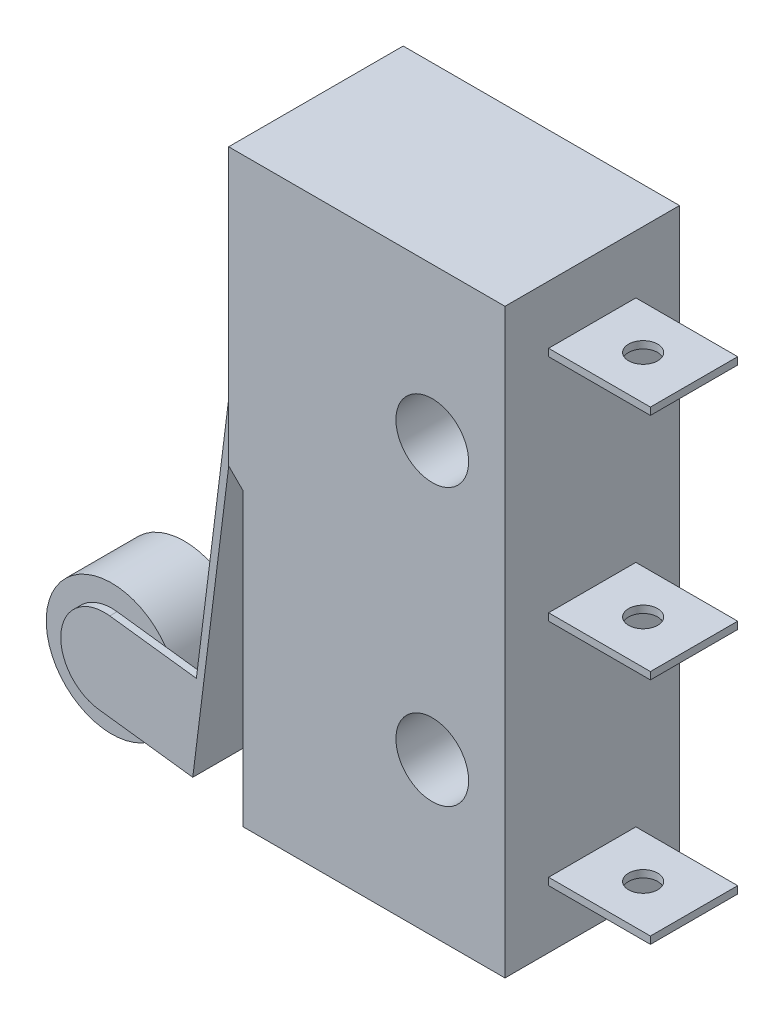
SolidWorks part; units mm, degrees
ref_plane "Front" through (0, 0, 0) normal (0, 0, 1) x (1, 0, 0)
ref_plane "Top" through (0, 0, 0) normal (0, 1, 0) x (1, 0, 0)
ref_plane "Right" through (0, 0, 0) normal (1, 0, 0) x (0, 0, -1)
sketch "Эскиз1" plane through (0, 0, 0) normal (0, 0, 1) x (1, 0, 0)
  line L0 (0, 0) -> (0, 10)
  line L1 (0, 0) -> (9, 0)
  line L2 (0, 20) -> (9, 20)
  line L3 (9, 0) -> (9, 20)
  line L4 (9, 10) -> (0, 10) construction
  line L5 (0, 10) -> (-0.5, 10.5)
  line L6 (-0.5, 10.5) -> (-0.5, 20)
  line L7 (0, 20) -> (-0.5, 20)
  circle A0 centre (6.5, 5.25) radius 1.25
  circle A1 centre (6.5, 14.75) radius 1.25
  dimension "D3" = 2.5
  dimension "D4" = 5.25
  dimension "D5" = 2.5
  dimension "D1" = 20
  dimension "D2" = 9
  dimension "D6" = 0.5
  dimension "D7" = 0.5
  dimension "D8" = 10
extrude "Бобышка-Вытянуть1" add sketch "Эскиз1" along normal blind 6
sketch "Эскиз2" plane through (-0.5, 0, 0) normal (-1, 0, 0) x (0, 0, 1)
  line L0 (3, 20) -> (3, 10.5) construction
  line L1 (6, 20) -> (0, 20) construction
  line L2 (6, 10.5) -> (0, 10.5) construction
ref_plane "Плоскость1" through (0, 0, 3) normal (0, 0, -1) x (0, -1, 0)
sketch "Эскиз3" plane through (0, 0, 3) normal (0, 0, -1) x (0, -1, 0)
  line L0 (-17, 0.5) -> (-17, 1.0293)
  line L1 (-20, 0.5) -> (-10.5, 0.5) construction
  line L2 (-13, 0.5) -> (-13, 1.75) construction
  line L3 (-16.781, 1.2774) -> (-13, 1.75)
  line L4 (-13, 1.75) -> (0.861, 3.4826)
  line L5 (0.861, 3.4826) -> (0.892, 3.2346)
  line L6 (0.892, 3.2346) -> (-16.531, 1.0567)
  line L7 (-16.75, 0.5) -> (-16.75, 0.8086)
  line L8 (-17, 0.5) -> (-16.75, 0.5)
  arc A0 (-16.781, 1.2774) -> (-17, 1.0293) centre (-16.75, 1.0293) ccw
  arc A1 (-16.531, 1.0567) -> (-16.75, 0.8086) centre (-16.5, 0.8086) ccw
  point P13 (-17, 1.25)
  dimension "D8" = 0.25
  dimension "D1" = 3
  dimension "D2" = 0.75
  dimension "D3" = 7
  dimension "D4" = 1.25
  dimension "D5" = 18
  dimension "D6" = 0.25
  dimension "D7" = 0.25
extrude "Бобышка-Вытянуть2" add sketch "Эскиз3" along normal blind 1.5 and the other way blind 1.5
sketch "Эскиз4" plane through (0, 0, 4.5) normal (0, 0, 1) x (1, 0, 0)
  line L0 (-3.4826, -0.861) -> (-6.4595, -0.4889)
  line L1 (-3.4826, -0.861) -> (-1.2774, 16.781) construction
  line L2 (-3.1105, 2.1158) -> (-6.0874, 2.4879)
  line L4 (-3.1105, 2.1158) -> (-3.4826, -0.861)
  line L5 (-3.2966, 0.6274) -> (-7.7618, 1.1856) construction
  arc A0 (-6.0874, 2.4879) -> (-6.4595, -0.4889) centre (-6.2734, 0.9995) ccw
  dimension "D4" = 1.5
  dimension "D1" = 3
  dimension "D2" = 3
extrude "Бобышка-Вытянуть3" add sketch "Эскиз4" against normal blind 0.25
mirror "Зеркальное отражение1" about plane through (0, 0, 3) normal (0, 0, -1) of "Бобышка-Вытянуть3"
sketch "Эскиз5" plane through (0, 0, 4.25) normal (0, 0, -1) x (-1, 0, 0)
  circle A0 centre (6.2734, 0.9995) radius 2.25
  arc A1 (6.4595, -0.4889) -> (6.0874, 2.4879) centre (6.2734, 0.9995) ccw construction
  dimension "D1" = 4.5
extrude "Бобышка-Вытянуть4" add sketch "Эскиз5" along normal blind 2.5
sketch "Эскиз6" plane through (9, 0, 0) normal (1, 0, 0) x (0, 0, -1)
  line L0 (-3, 0) -> (-3, 20) construction
  line L1 (-6, 0) -> (0, 0) construction
  line L2 (-6, 20) -> (0, 20) construction
  line L3 (0, 10) -> (-6, 10) construction
  line L4 (-1.5, 2) -> (-4.5, 2)
  line L5 (-1.5, 2) -> (-1.5, 2.25)
  line L6 (-1.5, 2.25) -> (-4.5, 2.25)
  line L7 (-4.5, 2) -> (-4.5, 2.25)
  line L8 (-1.5, 2) -> (-4.5, 2.25) construction
  line L9 (-1.5, 2.25) -> (-4.5, 2) construction
  line L10 (0, 0) -> (0, 20) construction
  line L11 (-6, 0) -> (-6, 20) construction
  line L12 (-1.5, 17.75) -> (-4.5, 18) construction
  line L13 (-1.5, 18) -> (-4.5, 17.75) construction
  line L14 (-4.5, 18) -> (-4.5, 17.75)
  line L15 (-1.5, 17.75) -> (-4.5, 17.75)
  line L16 (-1.5, 18) -> (-1.5, 17.75)
  line L17 (-1.5, 18) -> (-4.5, 18)
  line L19 (-1.5, 10.125) -> (-4.5, 10.125)
  line L20 (-1.5, 10.125) -> (-1.5, 9.875)
  line L21 (-1.5, 9.875) -> (-4.5, 9.875)
  line L22 (-4.5, 10.125) -> (-4.5, 9.875)
  line L23 (-1.5, 10.125) -> (-4.5, 9.875) construction
  line L24 (-1.5, 9.875) -> (-4.5, 10.125) construction
  point P6 (-3, 2.125)
  point P21 (-3, 17.875)
  point P22 (-3, 10)
  dimension "D1" = 3
  dimension "D2" = 0.25
  dimension "D3" = 2
  dimension "D4" = 0.25
  dimension "D5" = 3
extrude "Бобышка-Вытянуть5" add sketch "Эскиз6" along normal blind 3.5
sketch "Эскиз7" plane through (0, 18, 0) normal (0, 1, 0) x (1, 0, 0)
  line L0 (10.75, -1.5) -> (10.75, -4.5) construction
  line L1 (12.5, -1.5) -> (9, -1.5) construction
  line L2 (12.5, -4.5) -> (9, -4.5) construction
  line L3 (12.5, -3) -> (9, -3) construction
  line L4 (12.5, -1.5) -> (12.5, -4.5) construction
  line L5 (9, -1.5) -> (9, -4.5) construction
  circle A0 centre (10.75, -3) radius 0.5
  dimension "D1" = 1
extrude "Вырез-Вытянуть1" cut sketch "Эскиз7" against normal through all
